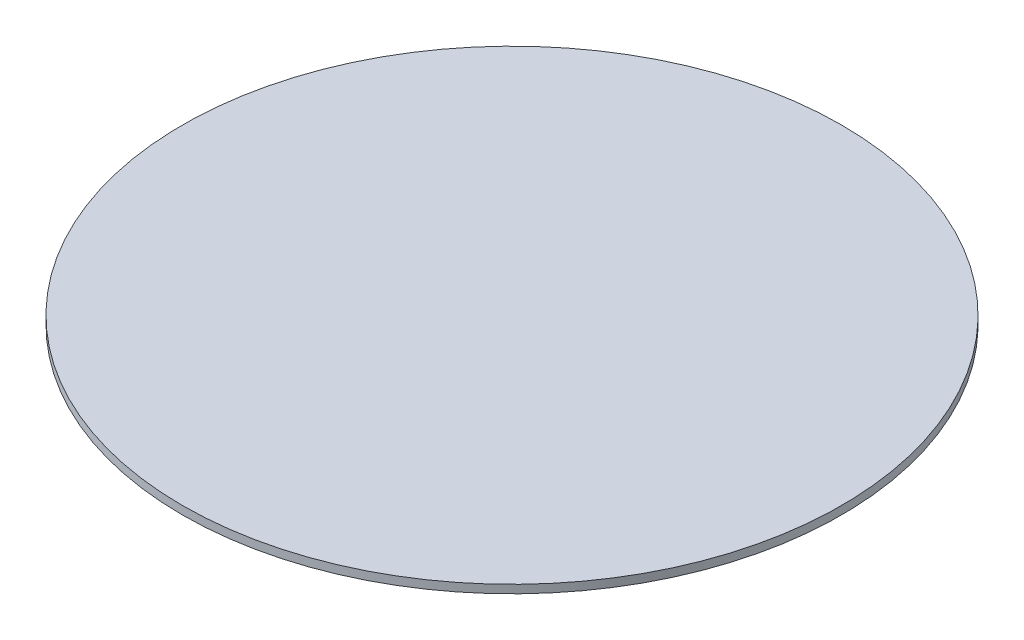
SolidWorks part; units mm, degrees
material "ABS PC"
ref_plane "Front Plane" through (0, 0, 0) normal (0, 0, 1) x (1, 0, 0)
ref_plane "Top Plane" through (0, 0, 0) normal (0, 1, 0) x (1, 0, 0)
ref_plane "Right Plane" through (0, 0, 0) normal (1, 0, 0) x (0, 0, -1)
sketch "Sketch1" plane through (0, 0, 0) normal (0, 1, 0) x (1, 0, 0)
  circle A0 centre (0, 0) radius 60
  dimension "D1" = 120
extrude "Boss-Extrude1" add sketch "Sketch1" along normal blind 1.5
